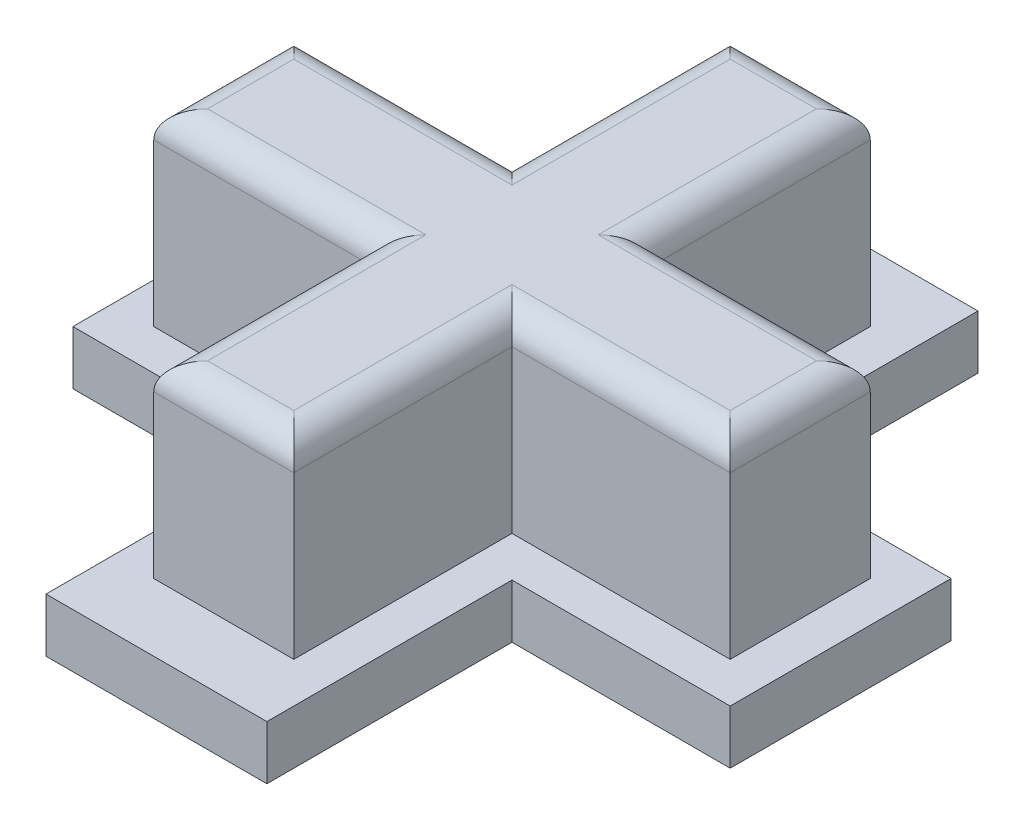
SolidWorks part; units mm, degrees
ref_plane "Front Plane" through (0, 0, 0) normal (0, 0, 1) x (1, 0, 0)
ref_plane "Top Plane" through (0, 0, 0) normal (0, 1, 0) x (1, 0, 0)
ref_plane "Right Plane" through (0, 0, 0) normal (1, 0, 0) x (0, 0, -1)
sketch "Sketch1" plane through (0, 0, 0) normal (0, 1, 0) x (1, 0, 0)
  line L0 (-4.1, 4.1) -> (-12.2, 4.1)
  line L1 (12.2, 4.1) -> (4.1, 4.1)
  line L2 (-12.2, 4.1) -> (-12.2, -4.1)
  line L3 (-12.2, -4.1) -> (-4.1, -4.1)
  line L4 (12.2, 4.1) -> (12.2, -4.1)
  line L5 (-12.2, 4.1) -> (12.2, -4.1) construction
  line L6 (-12.2, -4.1) -> (12.2, 4.1) construction
  line L7 (-4.1, 13.2) -> (4.1, 13.2)
  line L8 (-4.1, 13.2) -> (-4.1, 4.1)
  line L9 (12.2, -4.1) -> (4.1, -4.1)
  line L10 (4.1, 13.2) -> (4.1, 4.1)
  line L11 (-4.1, 13.2) -> (4.1, 4.1) construction
  line L12 (-4.1, 4.1) -> (4.1, 13.2) construction
  line L14 (-4.1, -4.1) -> (-4.1, -13.2)
  line L15 (-4.1, -13.2) -> (4.1, -13.2)
  line L16 (4.1, -4.1) -> (4.1, -13.2)
  line L17 (-4.1, -4.1) -> (4.1, -13.2) construction
  line L18 (-4.1, -13.2) -> (4.1, -4.1) construction
  line L19 (12.2, -4.1) -> (12.1894, -4.124)
  point P0 (0, 0)
  point P6 (0, 8.65)
  point P11 (0, -8.65)
  dimension "D1" = 24.4
  dimension "D2" = 8.2
  dimension "D3" = 8.2
  dimension "D4" = 0
  dimension "D5" = 8.1
  dimension "D6" = 9.1
  dimension "D7" = 9.1
  dimension "D8" = 8.2
  dimension "D9" = 8.1
  dimension "D10" = 0
extrude "Boss-Extrude1" add sketch "Sketch1" along normal blind 2 contours L16 L9 L4 L1 L10 L7 L8 L0 L2 L3 L14 L15
sketch "Sketch4" plane through (0, 2, 0) normal (0, 1, 0) x (1, 0, 0)
  line L0 (12.2, 4.1) -> (12.2, -4.1) construction
  line L1 (10.7, -2.6) -> (5.5, -2.6)
  line L2 (10.7, -2.6) -> (10.7, 2.6)
  line L3 (10.7, 2.6) -> (5.5, 2.6)
  line L4 (-2.6, 2.6) -> (-5.5, 2.6)
  line L5 (10.7, -2.6) -> (5.5, 2.6) construction
  line L6 (10.7, 2.6) -> (5.5, -2.6) construction
  line L7 (2.6, -10.7) -> (-2.6, -10.7)
  line L8 (2.6, -2.6) -> (2.6, -10.7)
  line L9 (-2.6, -2.6) -> (-2.6, -10.7)
  line L10 (2.6, 10.7) -> (2.6, 2.6)
  line L11 (-2.6, 10.7) -> (-2.6, 2.6)
  line L13 (-2.6, -2.6) -> (-10.7, -2.6)
  line L15 (2.6, 10.7) -> (-2.6, 10.7)
  line L21 (-5.5, 2.6) -> (-10.7, 2.6)
  line L22 (-10.7, -2.6) -> (-10.7, 2.6)
  line L23 (-5.5, -2.6) -> (-10.7, 2.6) construction
  line L24 (-5.5, 2.6) -> (-10.7, -2.6) construction
  line L25 (12.2, 4.1) -> (4.1, 4.1) construction
  line L27 (-4.1, 13.2) -> (4.1, 13.2) construction
  line L28 (-4.1, 4.1) -> (-12.2, 4.1) construction
  line L29 (5.5, -2.6) -> (2.6, -2.6)
  line L31 (-12.2, 4.1) -> (-12.2, -4.1) construction
  line L33 (-4.1, -13.2) -> (4.1, -13.2) construction
  line L37 (2.6, 2.6) -> (5.5, 2.6)
  point P0 (8.1, 0)
  point P15 (-8.1, 0)
  dimension "D1" = 5.2
  dimension "D2" = 5.2
  dimension "D3" = 1.5
  dimension "D4" = 1.5
  dimension "D6" = 5.2
  dimension "D7" = 5.2
  dimension "D8" = 21.4
  dimension "D12" = 2.5
  dimension "D13" = 1.5
  dimension "D14" = 1.5
  dimension "D16" = 2.5
  dimension "D17" = 21.4
extrude "Boss-Extrude3" add sketch "Sketch4" along normal blind 7
fillet "Fillet5" radius 1 12 edges at (-10.7, 9, 0) (-6.65, 9, -2.6) (0, 9, -10.7) (6.65, 9, -2.6) (10.7, 9, 0) (6.65, 9, 2.6) (0, 9, 10.7) (-6.65, 9, 2.6) (-2.6, 9, 6.65) (2.6, 9, 6.65) (-2.6, 9, -6.65) (2.6, 9, -6.65)
